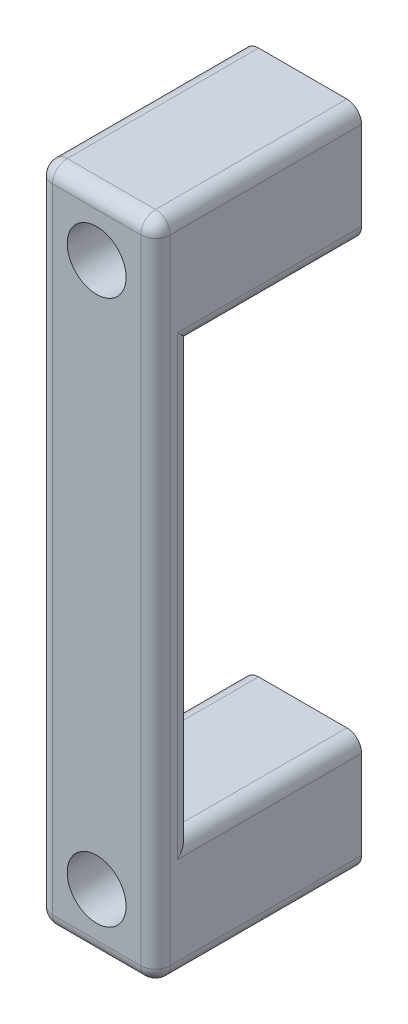
SolidWorks part; units mm, degrees
ref_plane "Front Plane" through (0, 0, 0) normal (0, 0, 1) x (1, 0, 0)
ref_plane "Top Plane" through (0, 0, 0) normal (0, 1, 0) x (1, 0, 0)
ref_plane "Right Plane" through (0, 0, 0) normal (1, 0, 0) x (0, 0, -1)
sketch "Sketch1" plane through (0, 0, 0) normal (0, 0, 1) x (1, 0, 0)
  line L1 (0, 0) -> (16, 0)
  line L2 (0, 0) -> (0, 90)
  line L3 (0, 90) -> (16, 90)
  line L4 (16, 0) -> (16, 90)
  circle A0 centre (8, 82) radius 2.2
  circle A1 centre (8, 8) radius 2.2
extrude "Boss-Extrude1" add sketch "Sketch1" along normal blind 28
sketch "Sketch2" plane through (16, 0, 0) normal (1, 0, 0) x (0, 0, -1)
  line L0 (0, 74) -> (-23, 74)
  line L1 (0, 0) -> (0, 90) construction
  line L2 (-23, 74) -> (-23, 16)
  line L3 (-23, 16) -> (0, 16)
  line L16 (0, 16) -> (0, 74)
extrude "Cut-Extrude1" cut sketch "Sketch2" against normal up to surface (16 mm away) up to face at (0, 45, 14)
sketch "Sketch3" plane through (0, 0, 28) normal (0, 0, 1) x (1, 0, 0)
  circle A0 centre (8, 82) radius 4
  circle A1 centre (8, 8) radius 4
extrude "Cut-Extrude2" cut sketch "Sketch3" against normal offset from surface (22 mm away) 6 up to face at (8, 8, 0)
fillet "Fillet1" radius 2 14 edges at (16, 90, 14) (16, 74, 11.5) (16, 45, 23) (16, 16, 11.5) (16, 0, 14) (16, 45, 28) (8, 0, 28) (0, 0, 14) (0, 16, 11.5) (0, 45, 23) (0, 74, 11.5) (8, 90, 28) (0, 90, 14) (0, 45, 28)
